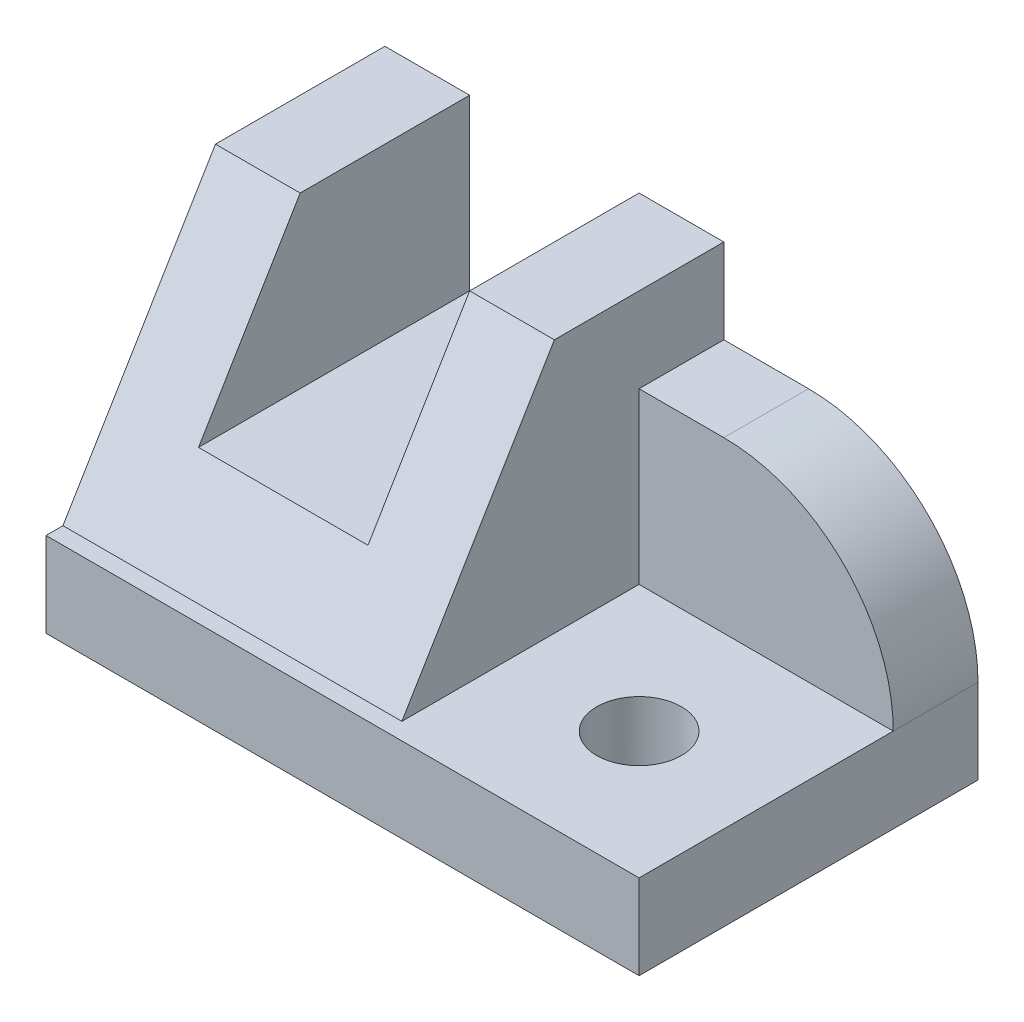
SolidWorks part; units mm, degrees
ref_plane "Front Plane" through (0, 0, 0) normal (0, 0, 1) x (1, 0, 0)
ref_plane "Top Plane" through (0, 0, 0) normal (0, 1, 0) x (1, 0, 0)
ref_plane "Right Plane" through (0, 0, 0) normal (1, 0, 0) x (0, 0, -1)
ref_plane "Plane1" through (0, 0, 0) normal (-1, 0, 0) x (0, -1, 0)
sketch "Sketch1" plane through (0, 0, 0) normal (-1, 0, 0) x (0, -1, 0)
  line L0 (-10, -2) -> (-40, -20)
  line L1 (-40, -20) -> (-10, -20)
  line L2 (-10, -20) -> (-10, -2)
  dimension "D1" = 30
  dimension "Width" = 18
extrude "Boss-Extrude1" add sketch "Sketch1" against normal blind 40
sketch "Sketch2" plane through (0, 0, -20) normal (0, 0, -1) x (-1, 0, 0)
  line L0 (-40, 40) -> (0, 40)
  line L1 (0, 40) -> (0, 10)
  line L2 (0, 10) -> (-40, 10)
  line L3 (-40, 10) -> (-40, 40)
extrude "Boss-Extrude2" add sketch "Sketch2" along normal blind 20
sketch "Sketch3" plane through (40, 0, 0) normal (1, 0, 0) x (0, 0, -1)
  line L0 (40, 10) -> (0, 10)
  line L1 (0, 10) -> (20, 40)
  line L2 (20, 40) -> (40, 40)
  line L3 (40, 40) -> (40, 10)
extrude "Boss-Extrude3" add sketch "Sketch3" along normal blind 30
sketch "Sketch4" plane through (70, 0, 0) normal (1, 0, 0) x (0, 0, -1)
  line L0 (20, 40) -> (0, 10)
  line L1 (0, 10) -> (30, 10)
  line L2 (30, 10) -> (30, 30)
  line L3 (30, 30) -> (40, 30)
  line L4 (40, 30) -> (40, 40)
  line L5 (40, 40) -> (20, 40)
extrude "Cut-Extrude1" cut sketch "Sketch4" against normal blind 30
sketch "Sketch5" plane through (0, 10, 0) normal (0, -1, 0) x (1, 0, 0)
  line L0 (70, 0) -> (70, -40)
  line L1 (70, -40) -> (0, -40)
  line L2 (0, -40) -> (0, 0)
  line L3 (0, 0) -> (70, 0)
extrude "Boss-Extrude4" add sketch "Sketch5" along normal blind 10
sketch "Sketch6" plane through (0, 0, -40) normal (0, 0, -1) x (-1, 0, 0)
  line L0 (-30, 40) -> (-30, 20)
  line L1 (-30, 20) -> (-10, 20)
  line L2 (-10, 20) -> (-10, 40)
  line L3 (-10, 40) -> (-30, 40)
extrude "Cut-Extrude2" cut sketch "Sketch6" against normal through all
hole_wizard "Ø10.0 (10) Diameter Hole1" positions "Sketch8" profile "Sketch7" hole size "Ø10.0" standard "ANSI Metric"
sketch "Sketch8" plane through (0, 0, 0) normal (0, -1, 0) x (-1, 0, 0)
  point P0 (-55, 15)
sketch "Sketch7" plane through (55, 0, -15) normal (1, 0, 0) x (0, 0, -1)
  line L0 (0, 0) -> (0, 40)
  line L1 (0, 40) -> (5, 40)
  line L2 (5, 40) -> (5, 0)
  line L5 (5, 0) -> (0, 0)
  line L11 (0, -6.35) -> (0, 107.95) construction
  dimension "Thru Hole Dia." = 10
  dimension "Thru Hole Depth" = 40
fillet "Fillet1" radius 20 1 edges at (70, 30, -35)
